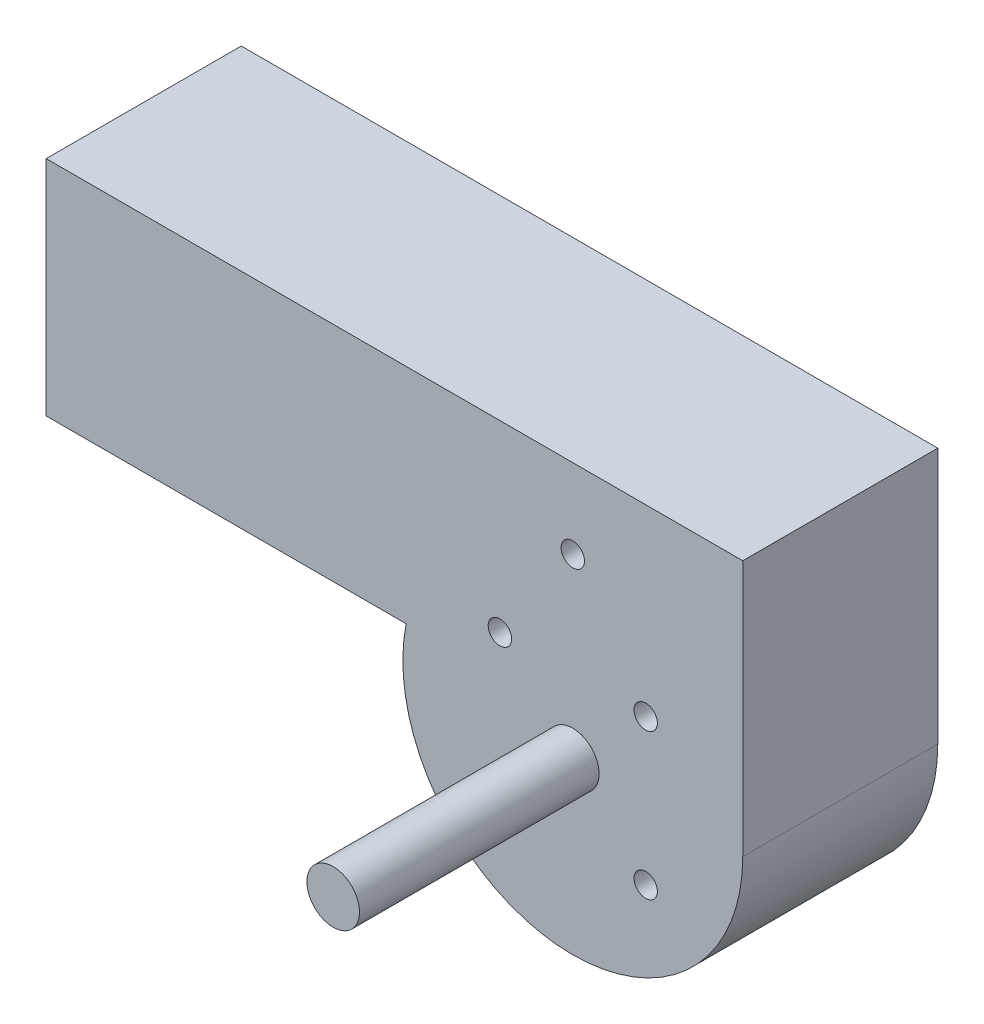
SolidWorks part; units mm, degrees
ref_plane "Front Plane" through (0, 0, 0) normal (0, 0, 1) x (1, 0, 0)
ref_plane "Top Plane" through (0, 0, 0) normal (0, 1, 0) x (1, 0, 0)
ref_plane "Right Plane" through (0, 0, 0) normal (1, 0, 0) x (0, 0, -1)
sketch "Sketch1" plane through (0, 0, 0) normal (0, 0, 1) x (1, 0, 0)
  line L0 (0, 0) -> (37, 0) construction
  line L1 (0, 0) -> (26.163, 26.163) construction
  line L2 (0, 0) -> (0, 63.5) construction
  line L4 (61, 0) -> (61, 92)
  line L5 (61, 92) -> (-189, 92)
  line L6 (-189, 92) -> (-189, 12)
  line L7 (-189, 12) -> (-59.808, 12)
  circle A0 centre (0, 0) radius 37 construction
  circle A2 centre (26.163, 26.163) radius 4.2
  circle A3 centre (26.163, -26.163) radius 4.2
  circle A4 centre (-26.163, -26.163) radius 4.2
  circle A5 centre (-26.163, 26.163) radius 4.2
  circle A6 centre (0, 63.5) radius 4.2
  arc A7 (-59.808, 12) -> (61, 0) centre (0, 0) ccw
  point P15 (0, 0)
  dimension "D1" = 74
  dimension "D2" = 45
  dimension "D3" = 4
  dimension "D5" = 92
  dimension "D4" = 63.5
  dimension "D6" = 250
  dimension "D7" = 80
extrude "Boss-Extrude1" add sketch "Sketch1" against normal blind 70 contours L7 A7 L4 L5 L6 | A5 | A6 | A2 | A3 | A4
sketch "Sketch2" plane through (0, 0, 0) normal (0, 0, 1) x (1, 0, 0)
  circle A0 centre (0, 0) radius 9.44
extrude "Boss-Extrude2" add sketch "Sketch2" along normal blind 86
